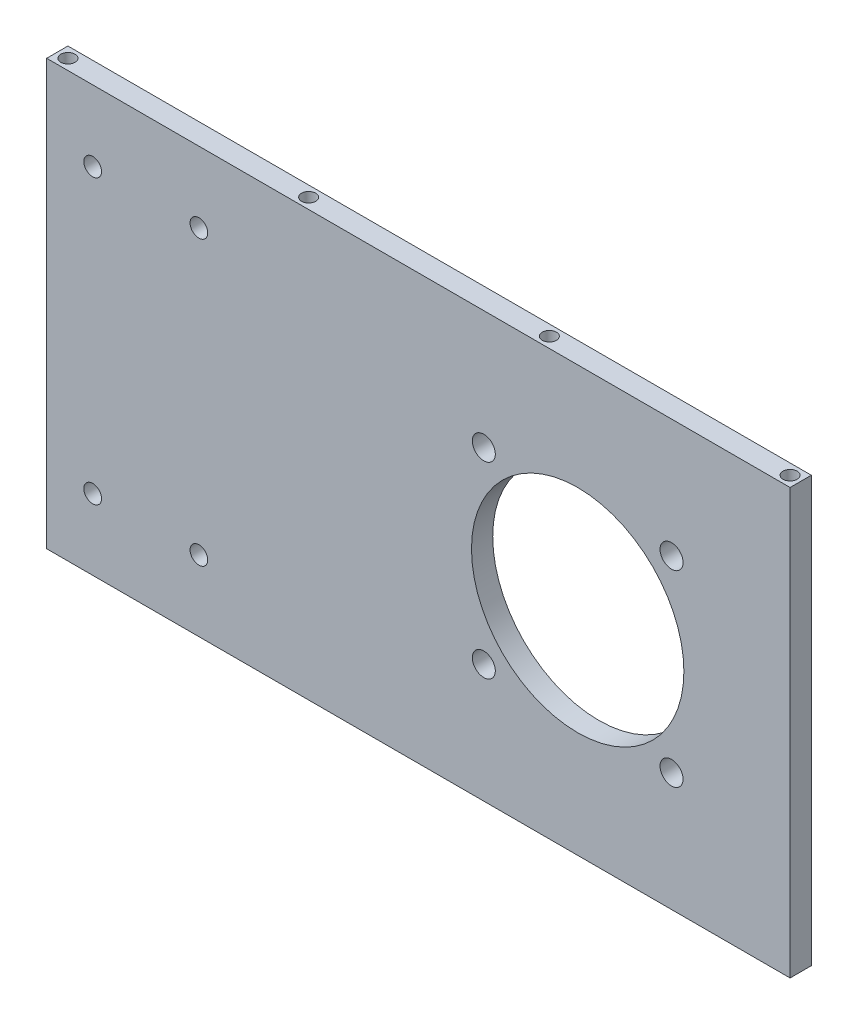
SolidWorks part; units mm, degrees
material "6061 合金"
ref_plane "前视基准面" through (0, 0, 0) normal (0, 0, 1) x (1, 0, 0)
ref_plane "上视基准面" through (0, 0, 0) normal (0, 1, 0) x (1, 0, 0)
ref_plane "右视基准面" through (0, 0, 0) normal (1, 0, 0) x (0, 0, -1)
sketch "草图1" plane through (0, 0, 0) normal (0, 0, 1) x (1, 0, 0)
  line L0 (0, 0) -> (26.5165, 26.5165) construction
  line L1 (0, 0) -> (91.6131, 0) construction
  line L2 (60, -60) -> (60, 60)
  line L3 (60, 60) -> (-150, 60)
  line L4 (-150, 60) -> (-150, -60)
  line L5 (60, -60) -> (-150, -60)
  circle A0 centre (26.5165, 26.5165) radius 3.25
  circle A1 centre (26.5165, -26.5165) radius 3.25
  circle A2 centre (-26.5165, -26.5165) radius 3.25
  circle A3 centre (-26.5165, 26.5165) radius 3.25
  circle A4 centre (0, 0) radius 30
  point P14 (0, 0)
  point P18 (60, 0)
  point P19 (-150, 0)
  dimension "D1" = 45
  dimension "D3" = 6.5
  dimension "D5" = 60
  dimension "D8" = 60
  dimension "D2" = 37.5
  dimension "D6" = 120
  dimension "D7" = 150
  dimension "D4" = 4
extrude "凸台-拉伸1" add sketch "草图1" along normal blind 6
sketch "草图2" plane through (0, 0, 6) normal (0, 0, 1) x (1, 0, 0)
  line L0 (60, 60) -> (-150, 60) construction
  line L1 (-150, 60) -> (-150, -60) construction
  line L2 (-107, 40) -> (-107, -40) construction
  line L3 (-107, -40) -> (-137, -40) construction
  line L4 (-137, -40) -> (-137, 40) construction
  line L5 (-137, 40) -> (-107, 40) construction
  circle A0 centre (-137, 40) radius 2.5
  circle A1 centre (-107, 40) radius 2.5
  circle A2 centre (-107, -40) radius 2.5
  circle A3 centre (-137, -40) radius 2.5
  dimension "D1" = 5
  dimension "D2" = 20
  dimension "D3" = 13
  dimension "D4" = 2
  dimension "D5" = 2
extrude "切除-拉伸1" cut sketch "草图2" against normal blind 10
sketch "草图3" plane through (0, -60, 0) normal (0, -1, 0) x (-1, 0, 0)
  line L0 (150, 0) -> (-60, 0) construction
  line L1 (-60, -6) -> (-60, 0) construction
  circle A0 centre (-57, -3) radius 2
  circle A1 centre (11, -3) radius 2
  circle A2 centre (79, -3) radius 2
  circle A3 centre (147, -3) radius 2
  dimension "D1" = 3
  dimension "D2" = 3
  dimension "D3" = 4
extrude "切除-拉伸2" cut sketch "草图3" against normal blind 20
ref_plane "基准面1" through (0, 0, 0) normal (0, -1, 0) x (-1, 0, 0)
mirror "镜向3" about plane through (0, 0, 0) normal (0, -1, 0) of "切除-拉伸2"
